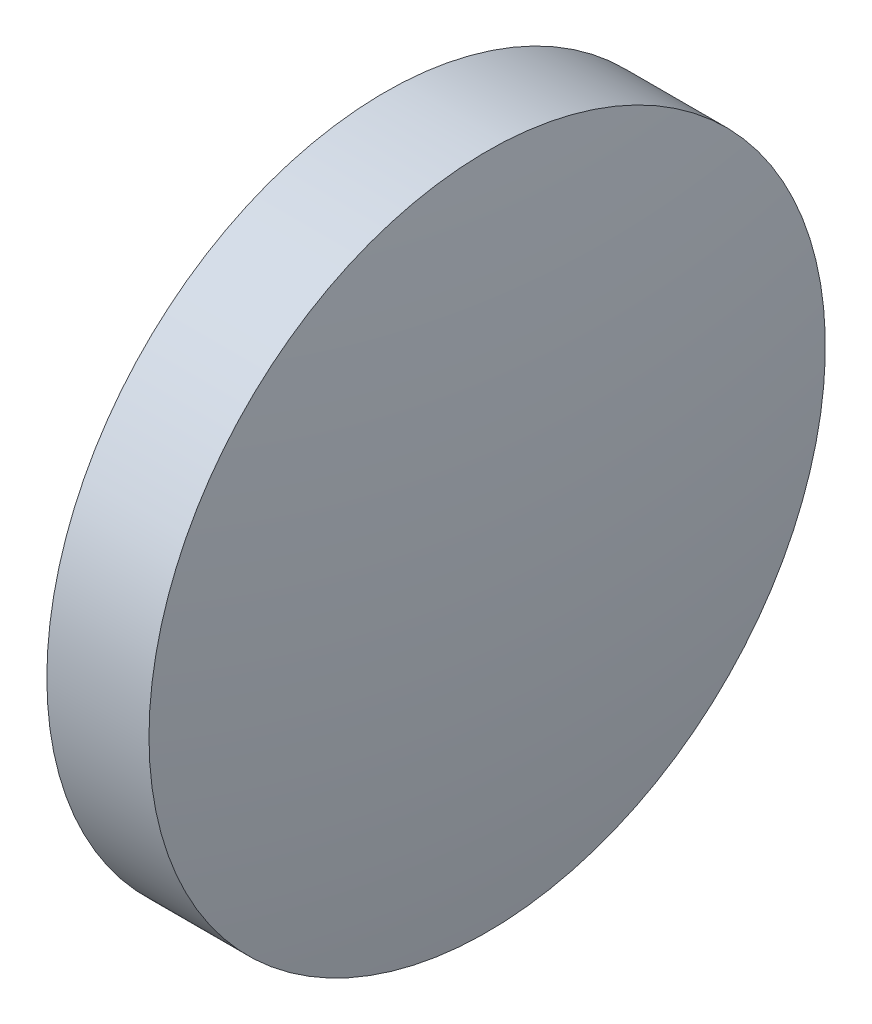
SolidWorks part; units mm, degrees
ref_plane "前视基准面" through (0, 0, 0) normal (0, 0, 1) x (1, 0, 0)
ref_plane "上视基准面" through (0, 0, 0) normal (0, 1, 0) x (1, 0, 0)
ref_plane "右视基准面" through (0, 0, 0) normal (1, 0, 0) x (0, 0, -1)
sketch "草图1" plane through (0, 0, 0) normal (0, 0, 1) x (1, 0, 0)
  line L0 (1088.5914, 408.4047) -> (1090.4914, 408.4047)
  line L4 (1087.3599, 408.4047) -> (1092.7382, 408.4047) construction
  line L5 (1088.5914, 408.4047) -> (1088.5914, 413.4047)
  line L7 (1088.5914, 413.4047) -> (1090.1014, 413.4047)
  arc A1 (1090.4914, 408.4047) -> (1090.1014, 413.4047) centre (1058.2505, 408.4052) ccw
revolve "旋转1" add sketch "草图1" angle 360 about L4
